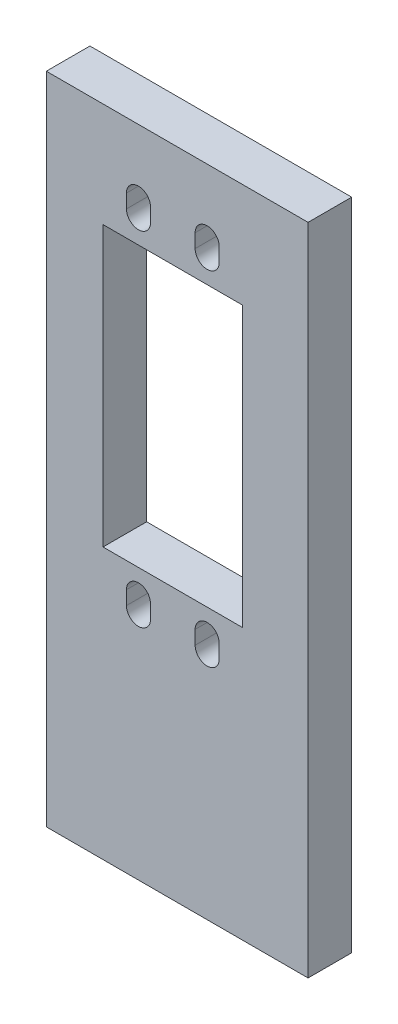
SolidWorks part; units mm, degrees
ref_plane "Front Plane" through (0, 0, 0) normal (0, 0, 1) x (1, 0, 0)
ref_plane "Top Plane" through (0, 0, 0) normal (0, 1, 0) x (1, 0, 0)
ref_plane "Right Plane" through (0, 0, 0) normal (1, 0, 0) x (0, 0, -1)
sketch "Sketch1" plane through (0, 0, 0) normal (0, 0, 1) x (1, 0, 0)
  line L1 (0, 0) -> (38.1, 0)
  line L2 (0, 0) -> (0, 95.25)
  line L3 (0, 95.25) -> (38.1, 95.25)
  line L4 (38.1, 0) -> (38.1, 95.25)
  dimension "D1" = 95.25
  dimension "D2" = 38.1
extrude "Boss-Extrude1" add sketch "Sketch1" along normal blind 6.35
sketch "Sketch2" plane through (0, 0, 0) normal (0, 0, -1) x (-1, 0, 0)
  line L0 (-38.1, 95.25) -> (0, 95.25) construction
  line L1 (-38.1, 88.9) -> (-38.1, 6.35) construction
  line B0 (-8.255, 80.045) -> (-8.255, 39.405)
  line B1 (-8.255, 80.045) -> (-28.575, 80.045)
  line B2 (-28.575, 80.045) -> (-28.575, 39.405)
  line B3 (-8.255, 39.405) -> (-28.575, 39.405)
  line B4 (-25.165, 83.725) -> (-25.165, 85.725)
  line B5 (-21.665, 83.725) -> (-21.665, 85.725)
  line B6 (-15.165, 83.725) -> (-15.165, 85.725)
  line B7 (-11.665, 83.725) -> (-11.665, 85.725)
  line B8 (-21.665, 35.725) -> (-21.665, 33.725)
  line B9 (-25.165, 35.725) -> (-25.165, 33.725)
  line B10 (-11.665, 35.725) -> (-11.665, 33.725)
  line B11 (-15.165, 35.725) -> (-15.165, 33.725)
  arc B12 (-25.165, 83.725) -> (-21.665, 83.725) centre (-23.415, 83.725) ccw
  arc B13 (-21.665, 85.725) -> (-25.165, 85.725) centre (-23.415, 85.725) ccw
  arc B14 (-15.165, 83.725) -> (-11.665, 83.725) centre (-13.415, 83.725) ccw
  arc B15 (-11.665, 85.725) -> (-15.165, 85.725) centre (-13.415, 85.725) ccw
  arc B16 (-21.665, 35.725) -> (-25.165, 35.725) centre (-23.415, 35.725) ccw
  arc B17 (-25.165, 33.725) -> (-21.665, 33.725) centre (-23.415, 33.725) ccw
  arc B18 (-11.665, 35.725) -> (-15.165, 35.725) centre (-13.415, 35.725) ccw
  arc B19 (-15.165, 33.725) -> (-11.665, 33.725) centre (-13.415, 33.725) ccw
  dimension "D1" = 9.525
  dimension "D2" = 9.525
sketch_block_instance "Block1-1"
sketch_block "Block1" parameters "D6"=1.75, "D1"=10, "D2"=48, "D3"=20.32, "D4"=40.64, "D5"=2, "D7"=14
extrude "Cut-Extrude1" cut sketch "Sketch2" against normal blind 6.35
